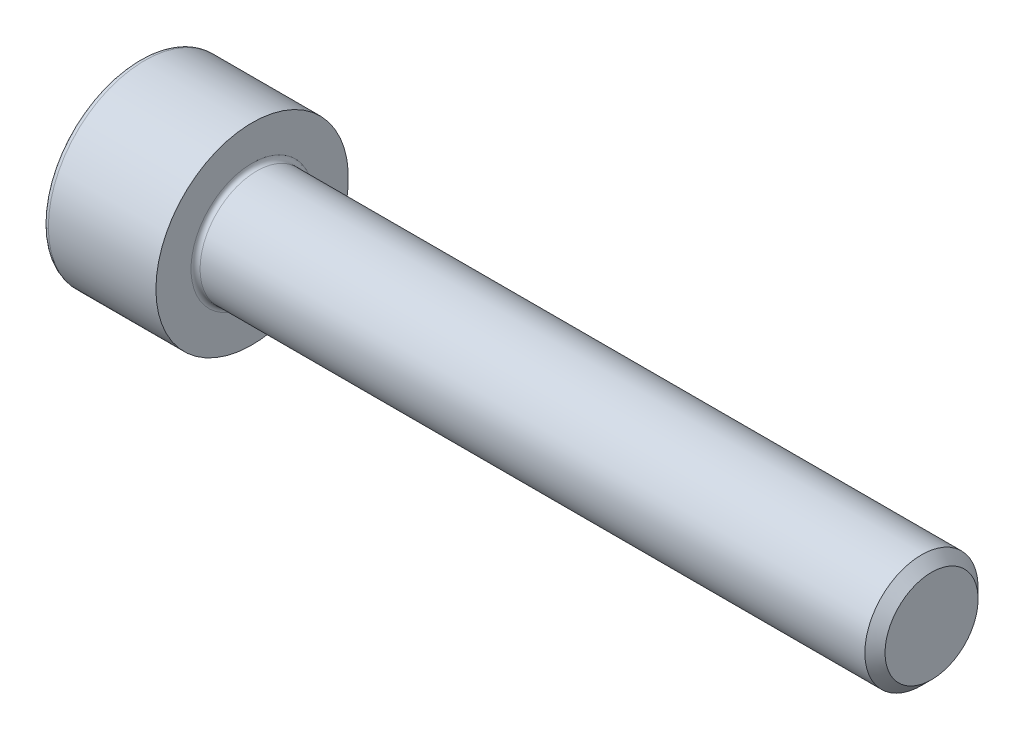
SolidWorks part; units mm, degrees
revolve "Base-Revolve" add sketch "BodySke"
sketch "BodySke" plane through (0, 0, 0) normal (0, 0, 1) x (1, 0, 0)
  line L0 (0, 0) -> (0, 4.25)
  line L1 (0, 4.25) -> (5, 4.25)
  line L2 (5, 4.25) -> (5, 2.5)
  line L3 (5, 2.5) -> (34.555, 2.5)
  line L4 (35, 2.055) -> (35, 0)
  line L5 (35, 0) -> (0, 0)
  line L6 (-31.75, 0) -> (127, 0) construction
  line L8 (35, 2.055) -> (34.555, 2.5)
  line L10 (35, -2.055) -> (34.555, -2.5) construction
  line L11 (5.8, 9.525) -> (5.8, 3.175) construction
  line L12 (13, 9.525) -> (13, 3.175) construction
  line L13 (-25, 9.525) -> (-25, 3.175) construction
  dimension "Body_ch_ang" = 45
  dimension "Thread_length" = 60
cosmetic thread "ThreadCosmetic"
fillet "Fillet1" radius 0.2 1 edges at (5, 0, 2.5)
fillet "Fillet2" radius 0.25 1 edges at (0, 0, 4.25)
ref_plane "Plane1" through (0, 0, 0) normal (0, 0, 1) x (1, 0, 0)
ref_plane "Plane2" through (0, 0, 0) normal (0, 1, 0) x (1, 0, 0)
ref_plane "Plane3" through (0, 0, 0) normal (1, 0, 0) x (0, 0, -1)
sketch "Sketch2" plane through (0, 0, 0) normal (0, 0, 1) x (1, 0, 0)
  line L0 (0, 2.042) -> (2.5, 2.042)
  line L1 (2.5, 2.042) -> (3.6789, 0)
  line L2 (-31.75, 0) -> (127, 0) construction
  line L3 (3.6789, 0) -> (0, 0)
  line L4 (0, 0) -> (0, 2.042)
  line L6 (0, 0) -> (47.625, 0) construction
  dimension "D2" = 60
revolve "Hex-PreBroach" cut sketch "Sketch2" angle 360 about L6
sketch "Sketch3" plane through (0, 0, 0) normal (-1, 0, 0) x (0, 0.5, 0.866)
  line L0 (1.1789, 2.042) -> (-1.1789, 2.042)
  line L1 (-1.1789, 2.042) -> (-2.3579, 0)
  line L2 (1.1789, 2.042) -> (2.3579, 0)
  line L3 (1.1789, -2.042) -> (2.3579, 0)
  line L4 (1.1789, -2.042) -> (-1.1789, -2.042)
  line L5 (-1.1789, -2.042) -> (-2.3579, 0)
extrude "Hex" cut sketch "Sketch3" against normal blind 2.5
sketch "ThdSchSke" plane through (0, 0, 0) normal (0, 0, 1) x (1, 0, 0)
  line L0 (13, -2.055) -> (12.6884, -2.5)
  line L1 (13, -2.055) -> (13.3116, -2.5)
  line L2 (13.3116, -2.5) -> (13.3116, -3.125)
  line L3 (-3.175, 0) -> (5.1513, 0) construction
  line L4 (0, 4) -> (0, -4) construction
  line L5 (13.3116, -3.125) -> (12.6884, -3.125)
  line L6 (12.6884, -3.125) -> (12.6884, -2.5)
revolve "ThreadSchematic" [suppressed] cut sketch "ThdSchSke" angle 360 about L3
pattern_linear "ThdSchPat" [suppressed]
equation "\"D2@Sketch3\" = \"Hex_size@Sketch3\" / 2"
equation "\"D1@Sketch3\" = \"Hex_size@Sketch3\" / 2"
equation "\"D1@Sketch2\" = \"Hex_size@Sketch3\" / 2"
equation "\"Thread_minor@ThreadCosmetic\"  =  \"Minor_dia@BodySke\""
equation "\"Depth@Sketch2\" =  \"Key_eng@Hex\""
equation "\"Thread_length@ThreadCosmetic\" = ((sgn( (\"Length@BodySke\" - \"Advance@BodySke\" * 3.0) - \"Thread_nom@BodySke\" )-1)*( (\"Length@BodySke\" - \"Advance@BodySke\" * 3.0) - \"Thread_nom@BodySke\" ))/-2+ \"Thread_nom@BodySke\""
equation "\"Thread_minor@ThdSchSke\" = \"Minor_dia@BodySke\""
equation "\"Diameter@ThdSchSke\" = \"Diameter@BodySke\""
equation "\"Overcut@ThdSchSke\" = \"Diameter@BodySke\" * 1.25"
equation "\"Start@ThdSchSke\" = \"Head_ht@BodySke\" + \"Length@BodySke\" - \"Thread_length@ThreadCosmetic\"  '---Non-countersunk---"
equation "\"Num_threads@ThdSchPat\" = int( \"Thread_length@ThreadCosmetic\" / \"Advance@BodySke\" + 0.999 )  + 1"
equation "\"Advance@ThdSchPat\" = \"Thread_length@ThreadCosmetic\" /  (\"Num_threads@ThdSchPat\" - 1) 'relax it"
equation "\"Num_threads@ThdSchPat\" = \"Num_threads@ThdSchPat\" - sgn( \"Num_threads@ThdSchPat\" - 1) '---chamfered tips only---"
